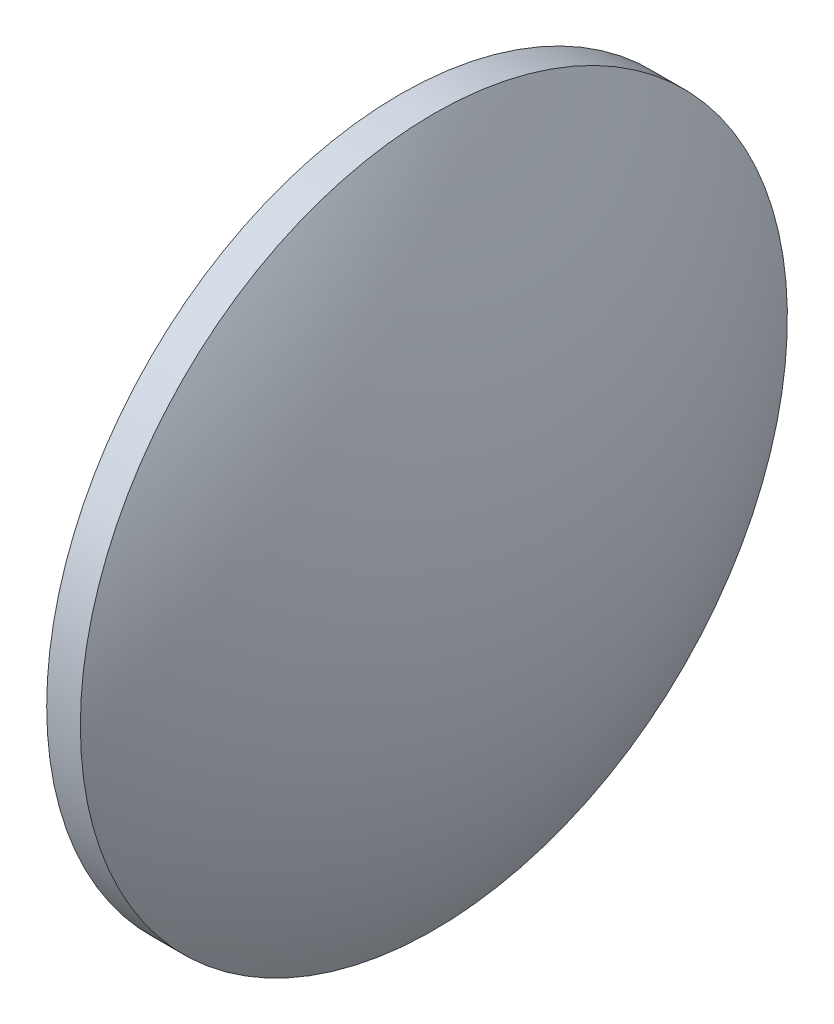
SolidWorks part; units mm, degrees
ref_plane "前视基准面" through (0, 0, 0) normal (0, 0, 1) x (1, 0, 0)
ref_plane "上视基准面" through (0, 0, 0) normal (0, 1, 0) x (1, 0, 0)
ref_plane "右视基准面" through (0, 0, 0) normal (1, 0, 0) x (0, 0, -1)
sketch "草图1" plane through (0, 0, 0) normal (0, 0, 1) x (1, 0, 0)
  line L0 (199.0064, 120.5838) -> (229.7434, 120.5838) construction
  line L1 (212.9444, 152.0839) -> (215.9444, 152.0839)
  line L2 (215.9444, 152.0839) -> (215.9444, 89.0836)
  line L3 (215.9444, 89.0836) -> (212.9444, 89.0836)
  line L4 (212.9444, 89.0836) -> (212.9444, 152.0839)
  arc A0 (212.9444, 152.0839) -> (212.9444, 89.0836) centre (265.6276, 120.5838) ccw
  arc A1 (215.9444, 89.0836) -> (215.9444, 152.0839) centre (163.2612, 120.5838) ccw
  dimension "D1" = 3
  dimension "D2" = 63.0003
revolve "旋转1" add sketch "草图1" angle 360 about L0
